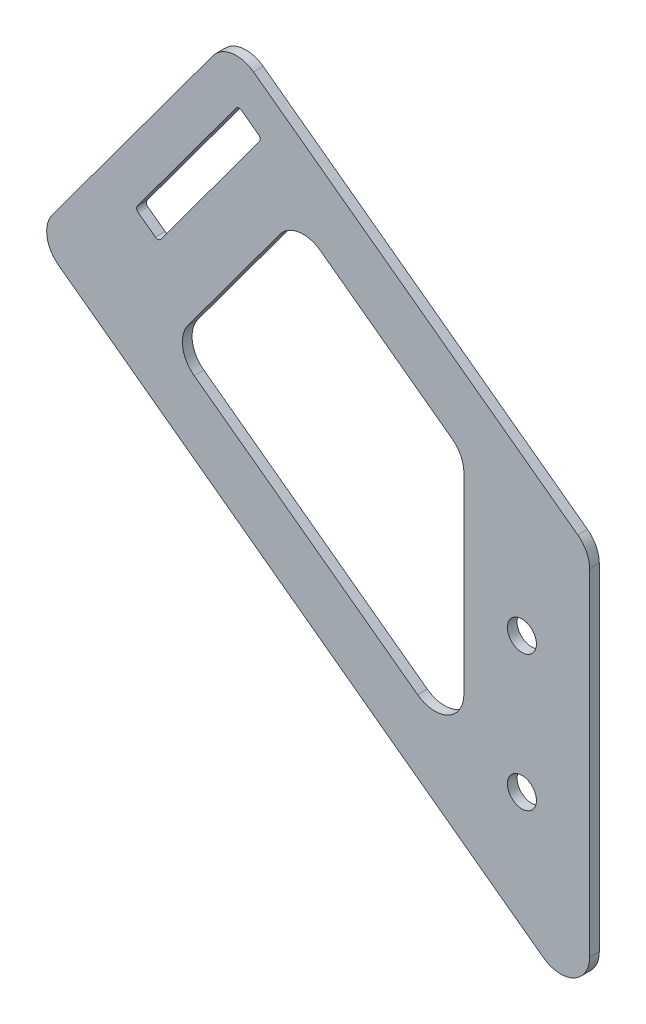
SolidWorks part; units mm, degrees
ref_plane "Front Plane" through (0, 0, 0) normal (0, 0, 1) x (1, 0, 0)
ref_plane "Top Plane" through (0, 0, 0) normal (0, 1, 0) x (1, 0, 0)
ref_plane "Right Plane" through (0, 0, 0) normal (1, 0, 0) x (0, 0, -1)
sketch "Sketch1" plane through (0, 0, 0) normal (0, 0, 1) x (1, 0, 0)
  line L1 (-154.8235, 399.6982) -> (-162.4926, 405.3473) construction
  line L4 (-155.8461, 400.4514) -> (-161.47, 404.594)
  line L5 (-129.3515, 450.3389) -> (-161.7394, 406.3698)
  line L6 (-121.9518, 446.4656) -> (-127.5758, 450.6082)
  line L7 (-35.56, 302.8376) -> (-35.56, 347.2876) construction
  line L9 (-154.0703, 400.7207) -> (-121.6825, 444.6898)
  line L13 (-154.8235, 399.6982) -> (-120.9293, 445.7124) construction
  line L15 (-13.335, 248.1566) -> (-13.335, 382.2315)
  line L16 (-10.16, 466.8115) -> (-10.16, 383.0274) construction
  line L17 (-13.335, 382.2315) -> (-131.2917, 469.1188)
  line L18 (-131.2917, 469.1188) -> (-195.3141, 382.2032)
  line L19 (-195.3141, 382.2032) -> (-13.335, 248.1566)
  line L20 (-109.3573, 429.3016) -> (-150.7836, 373.0621)
  line L21 (-109.3573, 429.3016) -> (-54.61, 388.9745)
  line L22 (-150.7836, 373.0621) -> (-96.0363, 332.735)
  line L23 (-54.61, 388.9745) -> (-96.0363, 332.735)
  line L24 (-54.61, 388.9745) -> (-54.61, 302.2202)
  line L25 (-54.61, 302.2202) -> (-96.0363, 332.735)
  circle A1 centre (-35.56, 347.2876) radius 4.7625 construction
  circle A2 centre (-35.56, 347.2876) radius 4.7625
  circle A3 centre (-35.56, 302.8376) radius 4.7625
  arc A8 (-129.3515, 450.3389) -> (-127.5758, 450.6082) centre (-128.329, 449.5857) cw
  arc A9 (-121.9518, 446.4656) -> (-121.6825, 444.6898) centre (-122.705, 445.443) cw
  arc A10 (-155.8461, 400.4514) -> (-154.0703, 400.7207) centre (-155.0929, 401.474) ccw
  arc A11 (-161.47, 404.594) -> (-161.7394, 406.3698) centre (-160.7168, 405.6166) cw
  circle A12 centre (-35.56, 302.8376) radius 4.7625 construction
  point P11 (-58.5827, 305.1465)
  point P20 (-135.9433, 484.2177)
  dimension "D1" = 3.175
  dimension "D5" = 19.05
  dimension "D6" = 1.27
  dimension "D2" = 12.7
  dimension "D3" = 38.1
  dimension "D4" = 12.7
  dimension "D7" = 9.525
  dimension "D8" = 57.15
  dimension "D9" = 19.05
  dimension "D10" = 19.05
  dimension "D11" = 19.05
extrude "Boss-Extrude1" add sketch "Sketch1" along normal blind 3.175
fillet "Fillet1" radius 9.525 8 edges at (-13.335, 248.1566, 1.5875) (-13.335, 382.2315, 1.5875) (-131.2917, 469.1188, 1.5875) (-195.3141, 382.2032, 1.5875) (-150.7836, 373.0621, 1.5875) (-54.61, 302.2202, 1.5875) (-54.61, 388.9745, 1.5875) (-109.3573, 429.3016, 1.5875)
